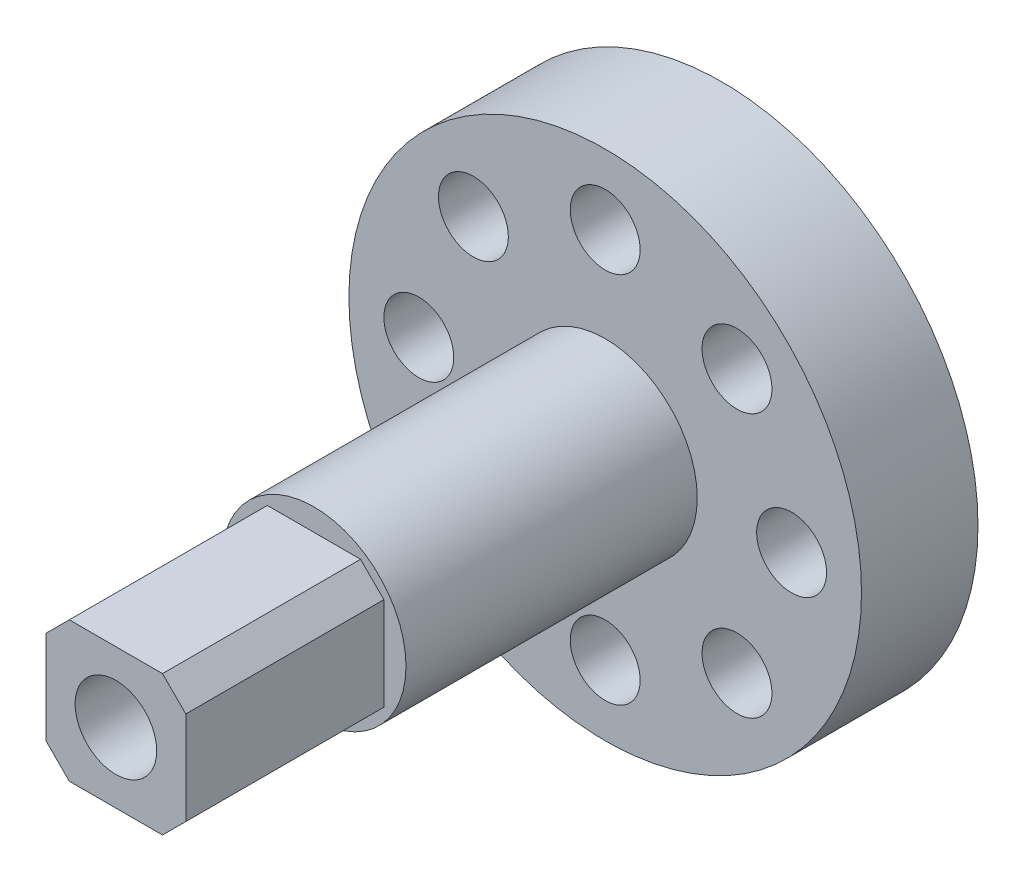
SolidWorks part; units mm, degrees
ref_plane "Plan de face" through (0, 0, 0) normal (0, 0, 1) x (1, 0, 0)
ref_plane "Plan de dessus" through (0, 0, 0) normal (0, 1, 0) x (1, 0, 0)
ref_plane "Plan de droite" through (0, 0, 0) normal (1, 0, 0) x (0, 0, -1)
sketch "Esquisse1" plane through (0, 0, 0) normal (0, 0, 1) x (1, 0, 0)
  circle A0 centre (0, 0) radius 4.5
  circle A1 centre (0, 0) radius 11
  dimension "D1" = 9
  dimension "D2" = 22
extrude "Boss.-Extru.1" add sketch "Esquisse1" along normal blind 4
sketch "Esquisse4" plane through (0, 0, 4) normal (0, 0, 1) x (1, 0, 0)
  circle A0 centre (0, 0) radius 11
  dimension "D1" = 22
extrude "Boss.-Extru.2" add sketch "Esquisse4" along normal blind 1
sketch "Esquisse2" plane through (0, 0, 5) normal (0, 0, 1) x (1, 0, 0)
  line L0 (0, 0) -> (8, 0) construction
  circle A0 centre (8, 0) radius 1.5
  circle A1 centre (5.6569, -5.6569) radius 1.5
  circle A2 centre (0, -8) radius 1.5
  circle A3 centre (-5.6569, -5.6569) radius 1.5
  circle A4 centre (-8, 0) radius 1.5
  circle A5 centre (-5.6569, 5.6569) radius 1.5
  circle A6 centre (0, 8) radius 1.5
  circle A7 centre (5.6569, 5.6569) radius 1.5
  point P4 (-8.721, 1.758)
  point P5 (0, 0)
  point P20 (0, 0)
  dimension "D2" = 3
  dimension "D1" = 8
  dimension "D3" = 8
extrude "Enlèv. mat.-Extru.1" cut sketch "Esquisse2" against normal through all both and the other way through all
sketch "Esquisse5" plane through (0, 0, 5) normal (0, 0, 1) x (1, 0, 0)
  line L0 (0, 0) -> (-3, 0) construction
  line L1 (-3, 3) -> (3, 3)
  line L2 (-3, 3) -> (-3, -3)
  line L3 (-3, -3) -> (3, -3)
  line L4 (3, 3) -> (3, -3)
  line L5 (0, 0) -> (0, 3) construction
  dimension "D1" = 6
extrude "Boss.-Extru.3" add sketch "Esquisse5" along normal blind 21
chamfer "Chanfrein1" distance 1 angle 45 4 edges at (-3, -3, 15.5) (3, -3, 15.5) (3, 3, 15.5) (-3, 3, 15.5)
sketch "Esquisse8" plane through (0, 0, 5) normal (0, 0, 1) x (1, 0, 0)
  circle A0 centre (0, 0) radius 3.95
  dimension "D1" = 7.9
extrude "Boss.-Extru.4" add sketch "Esquisse8" along normal blind 12.5
sketch "Esquisse6" plane through (0, 0, 26) normal (0, 0, 1) x (1, 0, 0)
  circle A0 centre (0, 0) radius 1.75
  dimension "D1" = 3.5
extrude "Enlèv. mat.-Extru.2" cut sketch "Esquisse6" against normal through all both and the other way through all
